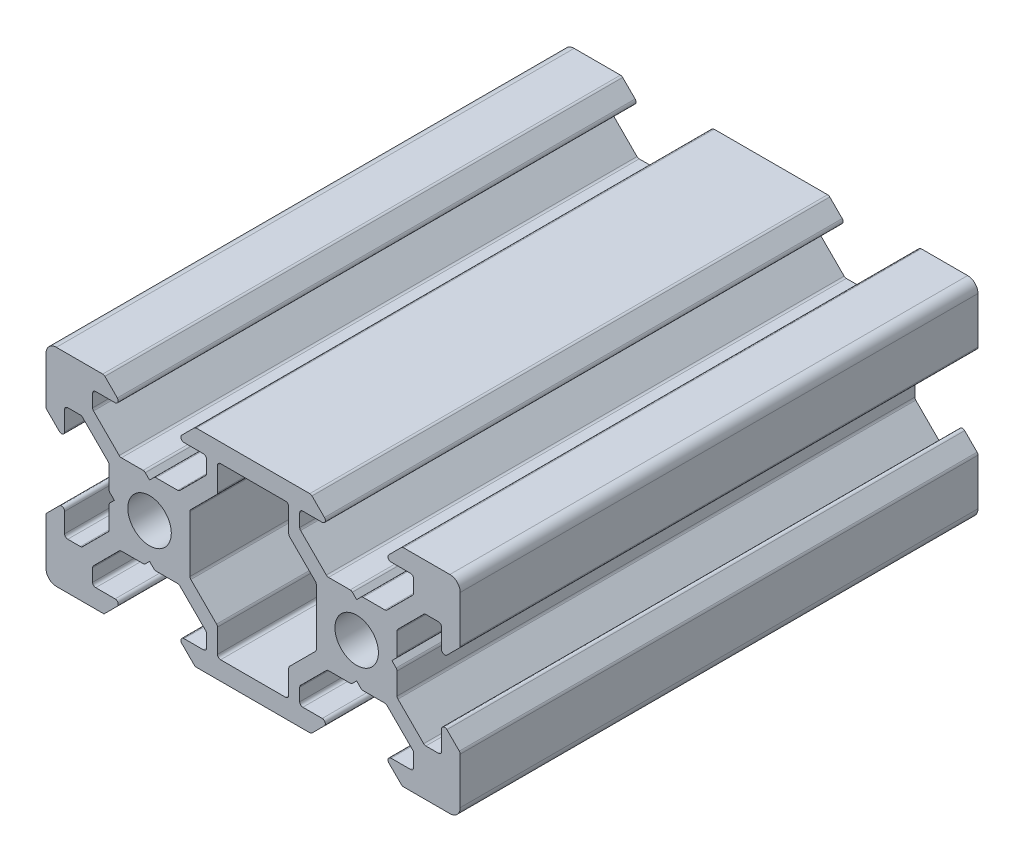
SolidWorks part; units mm, degrees
material "1060 Сплав"
ref_plane "Спереди" through (0, 0, 0) normal (0, 0, 1) x (1, 0, 0)
ref_plane "Сверху" through (0, 0, 0) normal (0, 1, 0) x (1, 0, 0)
ref_plane "Справа" through (0, 0, 0) normal (1, 0, 0) x (0, 0, -1)
sketch "Эскиз1" plane through (0, 0, 0) normal (0, 0, 1) x (1, 0, 0)
  line L0 (12.9654, 0) -> (-12.9654, 0) construction
  line L1 (0, -12.9654) -> (0, 12.9654) construction
  line L2 (0, 0) -> (-18.3359, -18.3359) construction
  line L3 (-10, -10) -> (-10, -4.4)
  line L4 (-10, -4.4) -> (-8.2, -2.6)
  line L5 (-8.2, -2.6) -> (-8.2, -5.4993)
  line L6 (-8.2, -5.4993) -> (-6.56, -5.4993)
  line L7 (-6.56, -5.4993) -> (-3.9007, -2.84)
  line L8 (-3.9007, -2.84) -> (-3.9007, -0.5)
  line L9 (-3.9007, -0.5) -> (-3.4007, 0)
  line L10 (-0.5, -3.9007) -> (0, -3.4007)
  line L11 (-2.84, -3.9007) -> (-0.5, -3.9007)
  line L12 (-5.4993, -6.56) -> (-2.84, -3.9007)
  line L13 (-5.4993, -8.2) -> (-5.4993, -6.56)
  line L14 (-2.6, -8.2) -> (-5.4993, -8.2)
  line L15 (-4.4, -10) -> (-2.6, -8.2)
  line L16 (-10, -10) -> (-4.4, -10)
  line L17 (-10, 10) -> (-4.4, 10)
  line L18 (-4.4, 10) -> (-2.6, 8.2)
  line L19 (-2.6, 8.2) -> (-5.4993, 8.2)
  line L20 (-5.4993, 8.2) -> (-5.4993, 6.56)
  line L21 (-5.4993, 6.56) -> (-2.84, 3.9007)
  line L22 (-2.84, 3.9007) -> (-0.5, 3.9007)
  line L23 (-0.5, 3.9007) -> (0, 3.4007)
  line L24 (-3.9007, 0.5) -> (-3.4007, 0)
  line L25 (-3.9007, 2.84) -> (-3.9007, 0.5)
  line L26 (-6.56, 5.4993) -> (-3.9007, 2.84)
  line L27 (-8.2, 5.4993) -> (-6.56, 5.4993)
  line L28 (-8.2, 2.6) -> (-8.2, 5.4993)
  line L29 (-10, 4.4) -> (-8.2, 2.6)
  line L30 (-10, 10) -> (-10, 4.4)
  line L31 (0.5, 3.9007) -> (0, 3.4007)
  line L32 (0.5, -3.9007) -> (0, -3.4007)
  line L33 (10, -10) -> (10, 10) construction
  line L34 (3.9007, -0.5) -> (3.9007, 0.5)
  line L35 (6.56, -5.4993) -> (6.56, -8.2)
  line L36 (13.44, -5.4993) -> (16.0993, -2.84)
  line L37 (6.56, 5.4993) -> (3.9007, 2.84)
  line L38 (3.9007, 2.84) -> (3.9007, 0.5)
  line L39 (6.56, -8.2) -> (13.44, -8.2)
  line L40 (2.84, 3.9007) -> (0.5, 3.9007)
  line L41 (5.4993, 6.56) -> (2.84, 3.9007)
  line L42 (5.4993, 8.2) -> (5.4993, 6.56)
  line L43 (2.6, 8.2) -> (5.4993, 8.2)
  line L44 (4.4, 10) -> (2.6, 8.2)
  line L45 (15.6, 10) -> (4.4, 10)
  line L46 (15.6, -10) -> (4.4, -10)
  line L47 (4.4, -10) -> (2.6, -8.2)
  line L48 (2.6, -8.2) -> (5.4993, -8.2)
  line L49 (5.4993, -8.2) -> (5.4993, -6.56)
  line L50 (5.4993, -6.56) -> (2.84, -3.9007)
  line L51 (2.84, -3.9007) -> (0.5, -3.9007)
  line L52 (6.56, 5.4993) -> (6.56, 8.2)
  line L53 (3.9007, -2.84) -> (3.9007, -0.5)
  line L54 (6.56, -5.4993) -> (3.9007, -2.84)
  line L55 (16.0993, -2.84) -> (16.0993, -0.5)
  line L56 (6.56, 8.2) -> (13.44, 8.2)
  line L57 (13.44, 5.4993) -> (13.44, 8.2)
  line L58 (17.16, -3.9007) -> (19.5, -3.9007)
  line L59 (14.5007, -6.56) -> (17.16, -3.9007)
  line L60 (14.5007, -8.2) -> (14.5007, -6.56)
  line L61 (17.4, -8.2) -> (14.5007, -8.2)
  line L62 (15.6, -10) -> (17.4, -8.2)
  line L63 (15.6, 10) -> (17.4, 8.2)
  line L64 (17.4, 8.2) -> (14.5007, 8.2)
  line L65 (14.5007, 8.2) -> (14.5007, 6.56)
  line L66 (14.5007, 6.56) -> (17.16, 3.9007)
  line L67 (17.16, 3.9007) -> (19.5, 3.9007)
  line L68 (16.0993, 2.84) -> (16.0993, 0.5)
  line L69 (13.44, 5.4993) -> (16.0993, 2.84)
  line L70 (13.44, -5.4993) -> (13.44, -8.2)
  line L71 (16.0993, -0.5) -> (16.0993, 0.5)
  line L72 (19.5, -3.9007) -> (20, -3.4007)
  line L73 (19.5, 3.9007) -> (20, 3.4007)
  line L74 (30, 10) -> (30, 4.4)
  line L75 (30, 4.4) -> (28.2, 2.6)
  line L76 (28.2, 2.6) -> (28.2, 5.4993)
  line L77 (28.2, 5.4993) -> (26.56, 5.4993)
  line L78 (26.56, 5.4993) -> (23.9007, 2.84)
  line L79 (23.9007, 2.84) -> (23.9007, 0.5)
  line L80 (23.9007, 0.5) -> (23.4007, 0)
  line L81 (20.5, 3.9007) -> (20, 3.4007)
  line L82 (22.84, 3.9007) -> (20.5, 3.9007)
  line L83 (25.4993, 6.56) -> (22.84, 3.9007)
  line L84 (25.4993, 8.2) -> (25.4993, 6.56)
  line L85 (22.6, 8.2) -> (25.4993, 8.2)
  line L86 (24.4, 10) -> (22.6, 8.2)
  line L87 (30, 10) -> (24.4, 10)
  line L88 (30, -10) -> (24.4, -10)
  line L89 (24.4, -10) -> (22.6, -8.2)
  line L90 (22.6, -8.2) -> (25.4993, -8.2)
  line L91 (25.4993, -8.2) -> (25.4993, -6.56)
  line L92 (25.4993, -6.56) -> (22.84, -3.9007)
  line L93 (22.84, -3.9007) -> (20.5, -3.9007)
  line L94 (20.5, -3.9007) -> (20, -3.4007)
  line L95 (23.9007, -0.5) -> (23.4007, 0)
  line L96 (23.9007, -2.84) -> (23.9007, -0.5)
  line L97 (26.56, -5.4993) -> (23.9007, -2.84)
  line L98 (28.2, -5.4993) -> (26.56, -5.4993)
  line L99 (28.2, -2.6) -> (28.2, -5.4993)
  line L100 (30, -4.4) -> (28.2, -2.6)
  line L101 (30, -10) -> (30, -4.4)
  circle A0 centre (0, 0) radius 2.1
  circle A1 centre (20, 0) radius 2.1
  point P62 (10, 8.2)
  point P80 (10, -8.2)
  dimension "D5" = 2.6
  dimension "D10" = 4.2
  dimension "D2" = 10
  dimension "D3" = 1.64
  dimension "D4" = 1.5
  dimension "D6" = 1.8
  dimension "D7" = 2.84
  dimension "D8" = 0.5
  dimension "D9" = 45
extrude "Бобышка-Вытянуть1" add sketch "Эскиз1" along normal blind 50
fillet "Скругление1" radius 1 4 edges at (-10, 10, 25) (-10, -10, 25) (30, 10, 25) (30, -10, 25)
fillet "Скругление2" radius 0.3 83 edges at (-4.4, 10, 25) (-2.6, 8.2, 25) (-5.4993, 8.2, 25) (-5.4993, 6.56, 25) (-2.84, 3.9007, 25) (-0.5, 3.9007, 25) (0.5, 3.9007, 25) (2.84, 3.9007, 25) (5.4993, 6.56, 25) (4.4, 10, 25) (5.4993, 8.2, 25) (2.6, 8.2, 25) (3.9007, 2.84, 25) (3.9007, -2.84, 25) (4.4, -10, 25) (2.6, -8.2, 25) (5.4993, -8.2, 25) (5.4993, -6.56, 25) (2.84, -3.9007, 25) (0.5, -3.9007, 25) (-0.5, -3.9007, 25) (-2.84, -3.9007, 25) (-5.4993, -6.56, 25) (-5.4993, -8.2, 25) (-2.6, -8.2, 25) (-10, -4.4, 25) (-8.2, -2.6, 25) (-8.2, -5.4993, 25) (-6.56, -5.4993, 25) (-3.9007, -2.84, 25) (-3.9007, -0.5, 25) (-3.9007, 0.5, 25) (-3.9007, 2.84, 25) (-6.56, 5.4993, 25) (-8.2, 5.4993, 25) (-8.2, 2.6, 25) (-10, 4.4, 25) (6.56, -5.4993, 25) (6.56, 5.4993, 25) (6.56, 8.2, 25) (13.44, 8.2, 25) (13.44, 5.4993, 25) (16.0993, 2.84, 25) (16.0993, -2.84, 25) (13.44, -5.4993, 25) (13.44, -8.2, 25) (6.56, -8.2, 25) (15.6, 10, 25) (17.4, 8.2, 25) (14.5007, 8.2, 25) (14.5007, 6.56, 25) (17.16, 3.9007, 25) (19.5, 3.9007, 25) (20.5, 3.9007, 25) (22.84, 3.9007, 25) (25.4993, 6.56, 25) (25.4993, 8.2, 25) (22.6, 8.2, 25) (24.4, 10, 25) (30, 4.4, 25) (28.2, 2.6, 25) (28.2, 5.4993, 25) (26.56, 5.4993, 25) (23.9007, 2.84, 25) (23.9007, 0.5, 25) (23.9007, -0.5, 25) (23.9007, -2.84, 25) (26.56, -5.4993, 25) (28.2, -5.4993, 25) (28.2, -2.6, 25) (30, -4.4, 25) (24.4, -10, 25) (22.6, -8.2, 25) (25.4993, -8.2, 25) (25.4993, -6.56, 25) (22.84, -3.9007, 25) (20.5, -3.9007, 25) (19.5, -3.9007, 25) (17.16, -3.9007, 25) (14.5007, -6.56, 25) (14.5007, -8.2, 25) (17.4, -8.2, 25) (15.6, -10, 25)
